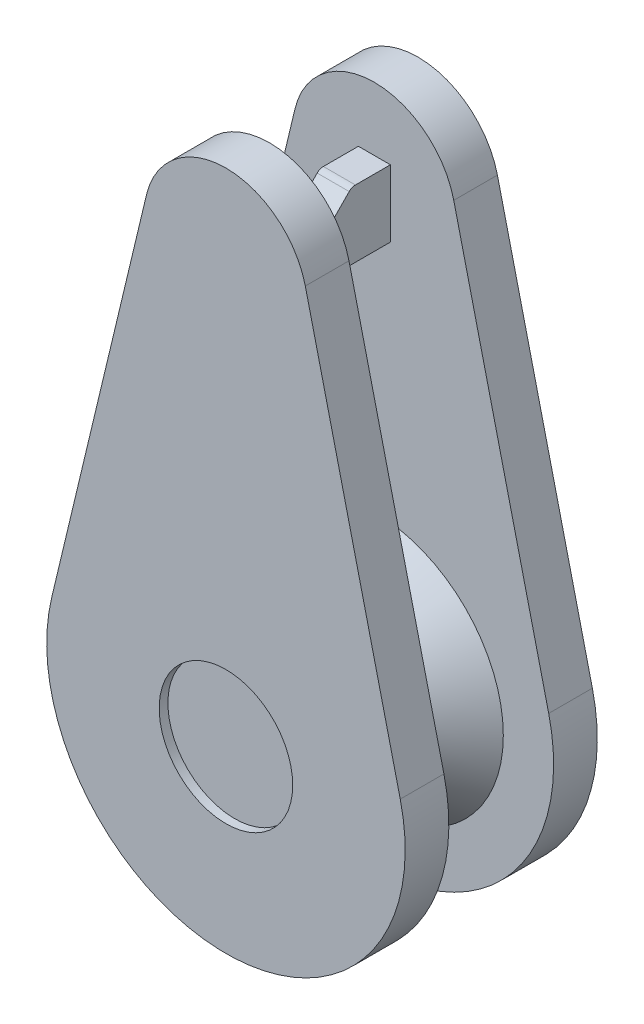
SolidWorks part; units mm, degrees
ref_plane "前视基准面" through (0, 0, 0) normal (0, 0, 1) x (1, 0, 0)
ref_plane "上视基准面" through (0, 0, 0) normal (0, 1, 0) x (1, 0, 0)
ref_plane "右视基准面" through (0, 0, 0) normal (1, 0, 0) x (0, 0, -1)
sketch "草图2" plane through (0, 0, 0) normal (0, 0, 1) x (1, 0, 0)
  line L0 (20.5077, 136.955) -> (22.6814, 146.0419)
  line L1 (26.3178, 146.0451) -> (28.4923, 136.955)
  arc A0 (20.5077, 136.955) -> (28.4923, 136.955) centre (24.5, 136) ccw
  arc A1 (22.6814, 146.0419) -> (26.3178, 146.0451) centre (24.5, 145.6069) cw
extrude "凸台-拉伸1" add sketch "草图2" along normal blind 1
sketch "草图3" plane through (0, 0, 1) normal (0, 0, 1) x (1, 0, 0)
  circle A0 centre (24.5, 136) radius 2.9527
ref_plane "基准面1" through (0, 0, 2.2) normal (0, 0, -1) x (-1, 0, 0)
sketch "草图5" plane through (0, 0, 2.2) normal (0, 0, -1) x (-1, 0, 0)
  circle A0 centre (-24.5, 136) radius 1.7382
loft "放样2" add profiles "草图3", "草图5"
sketch "草图6" plane through (0, 0, 1) normal (0, 0, 1) x (1, 0, 0)
  line L1 (24.1334, 146.0244) -> (24.8666, 146.0244)
  line L2 (24.1334, 146.0244) -> (24.1334, 144.4907)
  line L3 (24.1334, 144.4907) -> (24.8666, 144.4907)
  line L4 (24.8666, 146.0244) -> (24.8666, 144.4907)
  line L5 (24.1334, 146.0244) -> (24.8666, 144.4907) construction
  line L6 (24.1334, 144.4907) -> (24.8666, 146.0244) construction
  point P0 (24.5, 145.2576)
extrude "凸台-拉伸2" add sketch "草图6" along normal blind 2.4
sketch "草图7" plane through (24.1334, 0, 0) normal (-1, 0, 0) x (0, 0, 1)
  line L0 (1.8847, 146.0244) -> (3.4, 144.4907)
  line L1 (3.4, 146.0244) -> (1, 146.0244) construction
  line L2 (3.4, 144.4907) -> (3.4, 146.0244)
  line L3 (3.4, 146.0244) -> (1.8847, 146.0244)
extrude "切除-拉伸1" cut sketch "草图7" against normal blind 2.4
fillet "圆角1" radius 0.2 2 edges at (24.5, 144.4907, 3.4) (24.5, 146.0244, 1.8847)
mirror "镜向4" about plane through (0, 0, 2.2) normal (0, 0, -1) of "放样2", "凸台-拉伸1"
mirror "镜向5" about plane through (0, 0, 2.2) normal (0, 0, -1) of "凸台-拉伸1"
fillet "圆角2" radius 0.2 1 edges at (22.7618, 136, 2.2)
sketch "草图8" plane through (0, 0, 4.4) normal (0, 0, 1) x (1, 0, 0)
  circle A0 centre (24.5, 136) radius 1.5294
extrude "切除-拉伸3" cut sketch "草图8" against normal blind 0.2
sketch "草图9" plane through (0, 0, 0) normal (1, 0, 0) x (0, 0, -1)
  line L0 (-2.2, -4.5154) -> (-2.2, 4.5154) construction
  circle A0 centre (-2.2, 139.2511) radius 1
sketch "草图10" plane through (0, 0, 2.2) normal (0, 0, -1) x (-1, 0, 0)
  line L0 (-24.4984, 147.4768) -> (-24.5, 131.8951)
  line L1 (-24.5, 131.8951) -> (-24.4992, 139.6859)
  arc A0 (-22.6814, 146.0419) -> (-26.3178, 146.0451) centre (-24.5, 145.6069) ccw construction
  arc A1 (-28.4923, 136.955) -> (-20.5077, 136.955) centre (-24.5, 136) ccw construction
ref_plane "基准面2" through (24.5, 0, 0) normal (1, 0, 0) x (0, 0, -1)
sketch "草图11" plane through (24.5, 0, 0) normal (1, 0, 0) x (0, 0, -1)
  line L0 (-2.2, 139.2511) -> (-1.2, 139.2511)
  line L1 (-1.2, 139.2511) -> (-2.2, 140.2511)
  line L2 (-2.2, 140.2511) -> (-2.2, 139.2511)
  circle A0 centre (-2.2, 139.2511) radius 1
